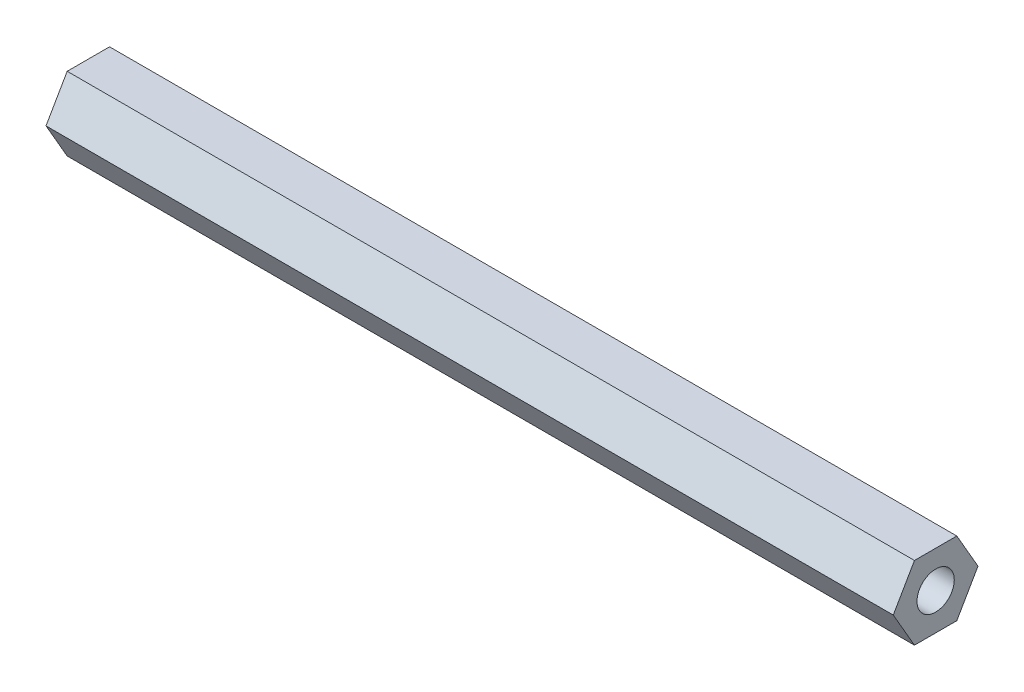
SolidWorks part; units mm, degrees
material "ABS"
ref_plane "Front Plane" through (0, 0, 0) normal (0, 0, 1) x (1, 0, 0)
ref_plane "Top Plane" through (0, 0, 0) normal (0, 1, 0) x (1, 0, 0)
ref_plane "Right Plane" through (0, 0, 0) normal (1, 0, 0) x (0, 0, -1)
sketch "Sketch1" plane through (0, 0, 0) normal (1, 0, 0) x (0, 0, -1)
  line L1 (1.25, 2.1651) -> (-1.25, 2.1651)
  line L2 (-1.25, 2.1651) -> (-2.5, 0)
  line L3 (-2.5, 0) -> (-1.25, -2.1651)
  line L4 (-1.25, -2.1651) -> (1.25, -2.1651)
  line L5 (1.25, -2.1651) -> (2.5, 0)
  line L6 (2.5, 0) -> (1.25, 2.1651)
  circle A0 centre (0, 0) radius 2.1651 construction
  circle A1 centre (0, 0) radius 1.1
  dimension "D2" = 2.2
  dimension "D1" = 5
extrude "Boss-Extrude1" add sketch "Sketch1" along normal blind 50
